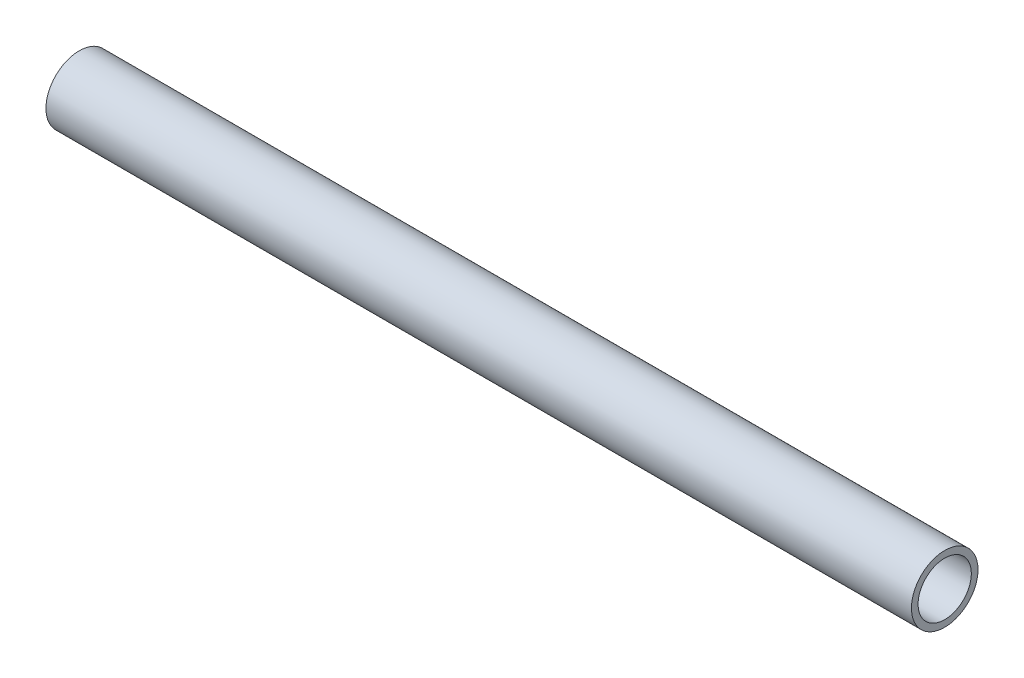
SolidWorks part; units mm, degrees
ref_plane "Front Plane" through (0, 0, 0) normal (0, 0, 1) x (1, 0, 0)
ref_plane "Top Plane" through (0, 0, 0) normal (0, 1, 0) x (1, 0, 0)
ref_plane "Right Plane" through (0, 0, 0) normal (1, 0, 0) x (0, 0, -1)
sketch "Sketch1" plane through (0, 0, 0) normal (0, 0, 1) x (1, 0, 0)
  line L0 (0, 0) -> (330.2, 0)
  dimension "D1" = 330.2
other "Tubing TUBING(1)"
ref_plane "Plane1" through (0, 0, 0) normal (1, 0, 0) x (0, 1, 0)
sketch "Sketch11" plane through (0, 0, 0) normal (1, 0, 0) x (0, 1, 0)
  circle A0 centre (0, 0) radius 12.7
  circle A1 centre (0, 0) radius 10.16
  point P5 (0, 12.7)
  point P6 (0, 10.16)
  point P7 (0, -12.7)
  point P8 (0, -10.16)
  point P9 (0, 0)
  dimension "D1" = 25.4
  dimension "D2" = 2.54
